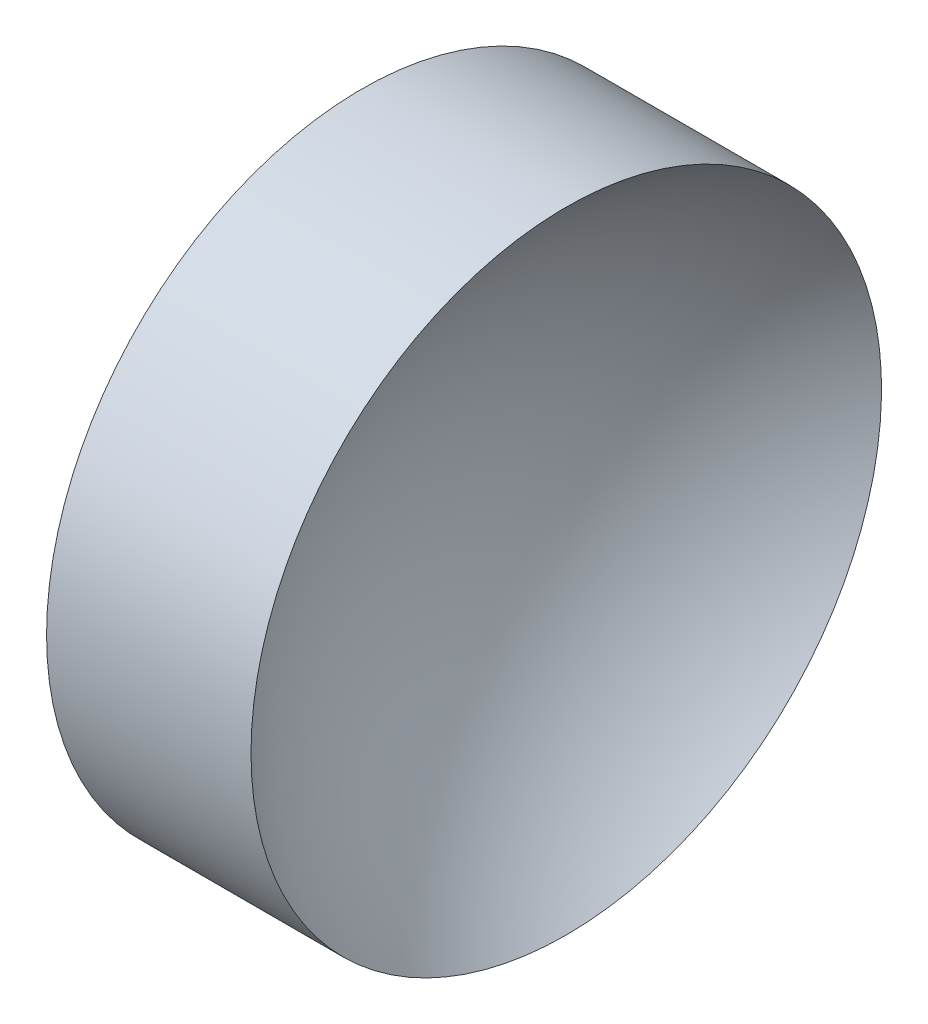
SolidWorks part; units mm, degrees
ref_plane "前视基准面" through (0, 0, 0) normal (0, 0, 1) x (1, 0, 0)
ref_plane "上视基准面" through (0, 0, 0) normal (0, 1, 0) x (1, 0, 0)
ref_plane "右视基准面" through (0, 0, 0) normal (1, 0, 0) x (0, 0, -1)
sketch "草图1" plane through (0, 0, 0) normal (0, 0, 1) x (1, 0, 0)
  line L0 (111.9552, 71.194) -> (132.4701, 71.194) construction
  line L1 (119.3629, 71.194) -> (119.3629, 83.894)
  line L2 (119.3629, 83.894) -> (127.599, 83.894)
  line L3 (121.3629, 71.194) -> (119.3629, 71.194)
  arc A0 (127.599, 83.894) -> (121.3629, 71.194) centre (137.4129, 71.194) ccw
revolve "旋转1" add sketch "草图1" angle 360 about L0
